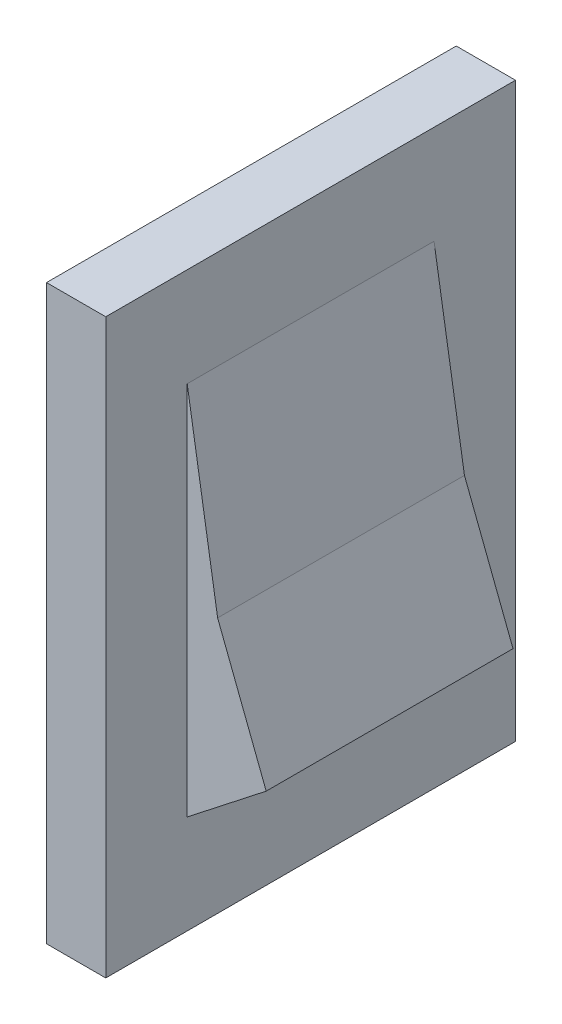
SolidWorks part; units mm, degrees
ref_plane "Front Plane" through (0, 0, 0) normal (0, 0, 1) x (1, 0, 0)
ref_plane "Top Plane" through (0, 0, 0) normal (0, 1, 0) x (1, 0, 0)
ref_plane "Right Plane" through (0, 0, 0) normal (1, 0, 0) x (0, 0, -1)
sketch "Sketch1" plane through (0, 0, 0) normal (1, 0, 0) x (0, 0, -1)
  line L1 (-5.2705, -7.366) -> (5.2705, -7.366)
  line L2 (-5.2705, -7.366) -> (-5.2705, 7.366)
  line L3 (-5.2705, 7.366) -> (5.2705, 7.366)
  line L4 (5.2705, -7.366) -> (5.2705, 7.366)
  line L5 (-5.2705, -7.366) -> (5.2705, 7.366) construction
  line L6 (-5.2705, 7.366) -> (5.2705, -7.366) construction
  point P0 (0, 0)
  dimension "D1" = 10.541
  dimension "D2" = 14.732
extrude "Boss-Extrude1" add sketch "Sketch1" along normal blind 1.524
sketch "Sketch2" plane through (1.524, 0, 0) normal (1, 0, 0) x (0, 0, -1)
  line L1 (-3.175, -4.826) -> (3.175, -4.826)
  line L2 (-3.175, -4.826) -> (-3.175, 4.826)
  line L3 (-3.175, 4.826) -> (3.175, 4.826)
  line L4 (3.175, -4.826) -> (3.175, 4.826)
  line L5 (-3.175, -4.826) -> (3.175, 4.826) construction
  line L6 (-3.175, 4.826) -> (3.175, -4.826) construction
  point P0 (0, 0)
  dimension "D1" = 6.35
  dimension "D2" = 9.652
extrude "Boss-Extrude2" add sketch "Sketch2" along normal blind 2.032
sketch "Sketch3" plane through (0, 0, 3.175) normal (0, 0, 1) x (1, 0, 0)
  line L0 (1.524, -4.826) -> (3.556, -3.2348)
  line L1 (3.556, 4.826) -> (3.556, -4.826) construction
  line L2 (3.556, -3.2348) -> (2.3066, 0)
  line L3 (2.3066, 0) -> (1.524, 4.826)
  line L4 (1.524, 4.826) -> (4.824, 4.826)
  line L5 (4.824, 4.826) -> (4.824, -4.826)
  line L6 (4.824, -4.826) -> (1.524, -4.826)
extrude "Cut-Extrude1" cut sketch "Sketch3" against normal up to surface (6.35 mm away) up to face at (2.54, 0, -3.175)
